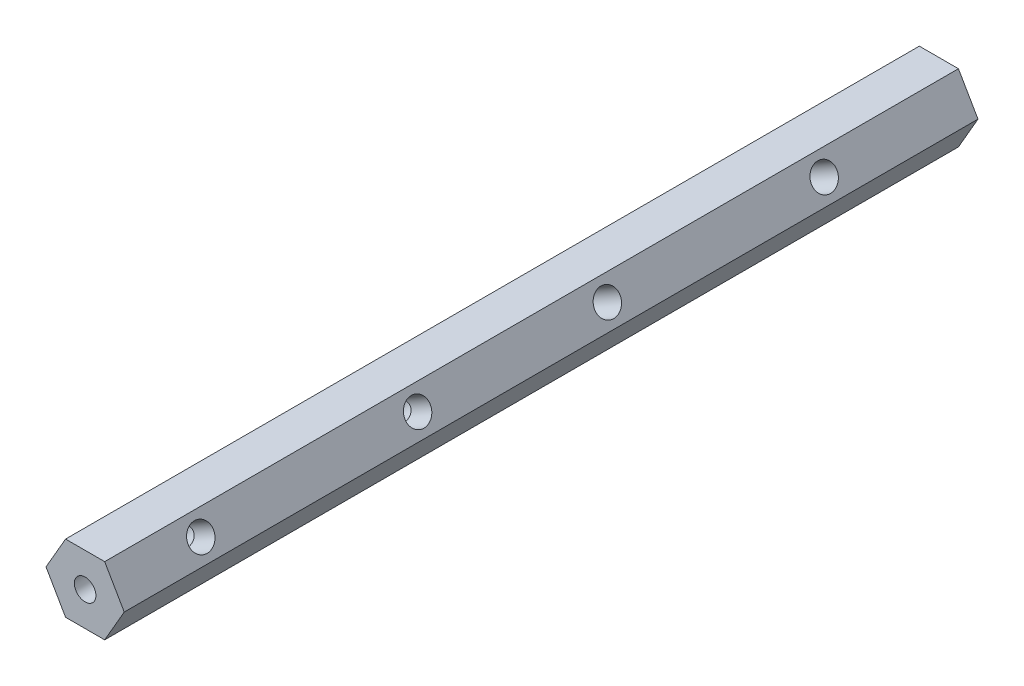
SolidWorks part; units mm, degrees
material "6061-T6 (SS)"
ref_plane "Front" through (0, 0, 0) normal (0, 0, 1) x (1, 0, 0)
ref_plane "Top" through (0, 0, 0) normal (0, 1, 0) x (1, 0, 0)
ref_plane "Right" through (0, 0, 0) normal (1, 0, 0) x (0, 0, -1)
sketch "Sketch1" plane through (0, 0, 0) normal (0, 0, 1) x (1, 0, 0)
  line L1 (7.3323, 0) -> (3.6662, 6.35)
  line L2 (3.6662, 6.35) -> (-3.6662, 6.35)
  line L3 (-3.6662, 6.35) -> (-7.3323, 0)
  line L4 (-7.3323, 0) -> (-3.6662, -6.35)
  line L5 (-3.6662, -6.35) -> (3.6662, -6.35)
  line L6 (3.6662, -6.35) -> (7.3323, 0)
  circle A0 centre (0, 0) radius 6.35 construction
  dimension "D1" = 12.7
extrude "Boss-Extrude1" add sketch "Sketch1" along normal blind 160.02
hole_wizard "#10-32 Tapped Hole1" positions "Sketch2" profile "Sketch4" tap size "#10-32" standard "ANSI Inch"
sketch "Sketch2" plane through (0, 0, 160.02) normal (0, 0, 1) x (1, 0, 0)
  point P0 (0, 0)
sketch "Sketch4" plane through (0, 0, 160.02) normal (1, 0, 0) x (0, -1, 0)
  line L0 (0, 0) -> (0, 77.4133)
  line L1 (0, 77.4133) -> (2.0193, 76.2)
  line L2 (2.0193, 76.2) -> (2.0193, 0)
  line L5 (2.0193, 0) -> (0, 0)
  line L10 (0, 77.4133) -> (-2.0193, 76.2) construction
  line L11 (0, -6.35) -> (0, 107.95) construction
  dimension "Tap Drill Dia." = 4.0386
  dimension "Tap Drill Depth" = 76.2
  dimension "Drill Angle" = 118
cosmetic thread "Hole Thread1" parameters "D1"=9.652, "D2"=4.826
sketch "Sketch5" plane through (5.4993, 3.175, 0) normal (0.866, 0.5, 0) x (0, 0, -1)
  line L0 (0, -3.6662) -> (0, 3.6662) construction
  circle A0 centre (-27.0002, 0) radius 2.3813
  circle A1 centre (-67.6402, 0) radius 2.3813
  circle A2 centre (-103.2002, 0) radius 2.3813
  circle A3 centre (-143.8402, 0) radius 2.3813
  point P10 (0, 0)
  dimension "D4" = 143.8402
  dimension "D5" = 4.7625
  dimension "D1" = 27.0002
  dimension "D2" = 67.6402
  dimension "D3" = 103.2002
extrude "Cut-Extrude1" cut sketch "Sketch5" against normal through all both and the other way through all
